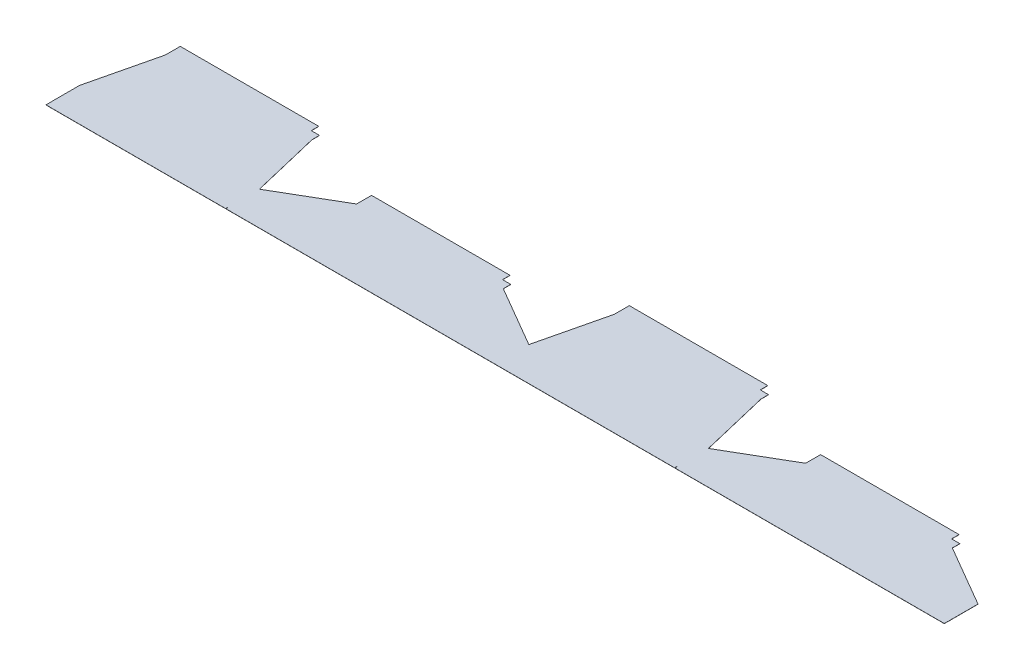
SolidWorks part; units mm, degrees
ref_plane "Front Plane" through (0, 0, 0) normal (0, 0, 1) x (1, 0, 0)
ref_plane "Top Plane" through (0, 0, 0) normal (0, 1, 0) x (1, 0, 0)
ref_plane "Right Plane" through (0, 0, 0) normal (1, 0, 0) x (0, 0, -1)
sketch "Sketch1" plane through (0, 0, 0) normal (0, 1, 0) x (1, 0, 0)
  line L0 (0, 0) -> (0, 12.7)
  line L1 (0, 12.7) -> (-0.254, 12.7)
  line L2 (-0.254, 12.7) -> (-0.254, 114.3)
  line L3 (-0.254, 114.3) -> (55.88, 348.9799)
  line L4 (55.88, 348.9799) -> (55.88, 399.7799)
  line L5 (55.88, 399.7799) -> (525.78, 399.7799)
  line L6 (525.78, 399.7799) -> (525.78, 374.3799)
  line L7 (525.78, 374.3799) -> (553.72, 374.3799)
  line L8 (553.72, 374.3799) -> (553.72, 348.9799)
  line L9 (553.72, 348.9799) -> (609.854, 114.3)
  line L10 (609.854, 114.3) -> (609.854, 12.7)
  line L11 (609.854, 12.7) -> (609.6, 12.7)
  line L12 (609.6, 12.7) -> (609.6, 0)
  line L13 (609.6, 0) -> (0, 0)
  line L14 (55.88, 348.9799) -> (609.854, 114.3) construction
  line L15 (553.72, 348.9799) -> (-0.254, 114.3) construction
  dimension "D1" = 0.254
  dimension "D2" = 12.7
  dimension "D3" = 609.6
  dimension "D4" = 241.3
  dimension "D5" = 101.6
  dimension "D6" = 497.84
  dimension "D7" = 27.94
  dimension "D8" = 50.8
  dimension "D9" = 25.4
sketch "Sketch3" plane through (0, 0, 0) normal (0, 1, 0) x (1, 0, 0)
  line L0 (610.108, 0) -> (610.108, 12.7)
  line L1 (610.108, 12.7) -> (609.854, 12.7)
  line L2 (609.854, 12.7) -> (609.854, 114.3)
  line L3 (609.854, 114.3) -> (818.388, 235.7054)
  line L4 (818.388, 235.7054) -> (818.388, 286.5054)
  line L5 (818.388, 286.5054) -> (1288.288, 286.5054)
  line L6 (1288.288, 286.5054) -> (1288.288, 261.1054)
  line L7 (1288.288, 261.1054) -> (1316.228, 261.1054)
  line L8 (1316.228, 261.1054) -> (1316.228, 235.7054)
  line L9 (1316.228, 235.7054) -> (1524.762, 114.3)
  line L10 (1524.762, 114.3) -> (1524.762, 12.7)
  line L11 (1524.762, 12.7) -> (1524.508, 12.7)
  line L12 (1524.508, 12.7) -> (1524.508, 0)
  line L13 (1524.508, 0) -> (610.108, 0)
  line L14 (818.388, 235.7054) -> (1524.762, 114.3) construction
  line L15 (1316.228, 235.7054) -> (609.854, 114.3) construction
  dimension "D1" = 0.254
  dimension "D2" = 12.7
  dimension "D3" = 914.4
  dimension "D4" = 241.3
  dimension "D5" = 101.6
  dimension "D6" = 497.84
  dimension "D7" = 27.94
  dimension "D8" = 50.8
  dimension "D9" = 25.4
extrude "Boss-Extrude1" add sketch "Sketch1" along normal blind 0.4572
extrude "Boss-Extrude2" add sketch "Sketch3" along normal up to surface (0.4572 mm away) up to face at (336.3686, 0.4572, -180.4057)
pattern_linear "LPattern1" count 2 spacing 1524 along (1, 0, 0) of "Boss-Extrude2", "Boss-Extrude1"
